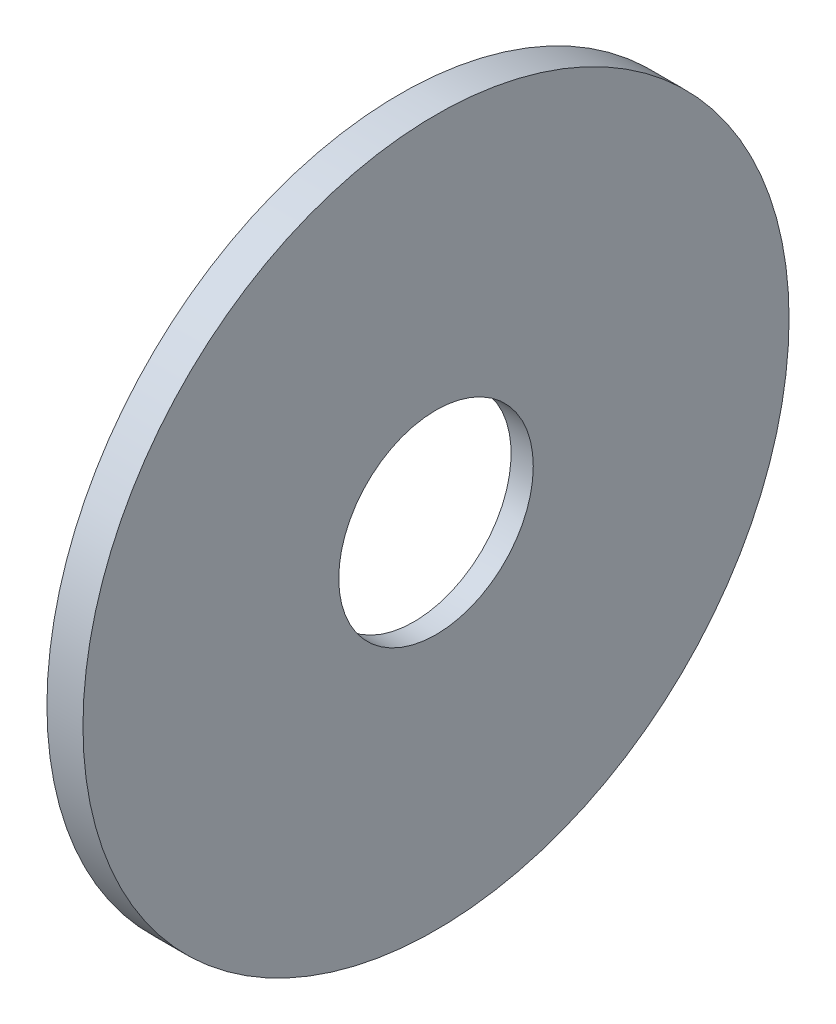
SolidWorks part; units mm, degrees
material "Glass"
ref_plane "Front Plane" through (0, 0, 0) normal (0, 0, 1) x (1, 0, 0)
ref_plane "Top Plane" through (0, 0, 0) normal (0, 1, 0) x (1, 0, 0)
ref_plane "Right Plane" through (0, 0, 0) normal (1, 0, 0) x (0, 0, -1)
sketch "Sketch1" plane through (0, 0, 0) normal (1, 0, 0) x (0, 0, -1)
  circle A0 centre (0, 0) radius 49
  circle A1 centre (0, 0) radius 13.5
  dimension "D1" = 98
  dimension "D2" = 27
extrude "Boss-Extrude1" add sketch "Sketch1" along normal blind 5
sketch "Sketch3" plane through (0, 0, 0) normal (0, 0, 1) x (1, 0, 0)
  line L0 (0, 0) -> (2, 0)
  line L1 (0, 49) -> (0, 0)
  line L2 (0, 49) -> (0, -49) construction
  arc A0 (2, 0) -> (0, 49) centre (-505.2355, 3.8373) ccw
revolve "Cut-Revolve1" cut sketch "Sketch3" angle 360 about L0
